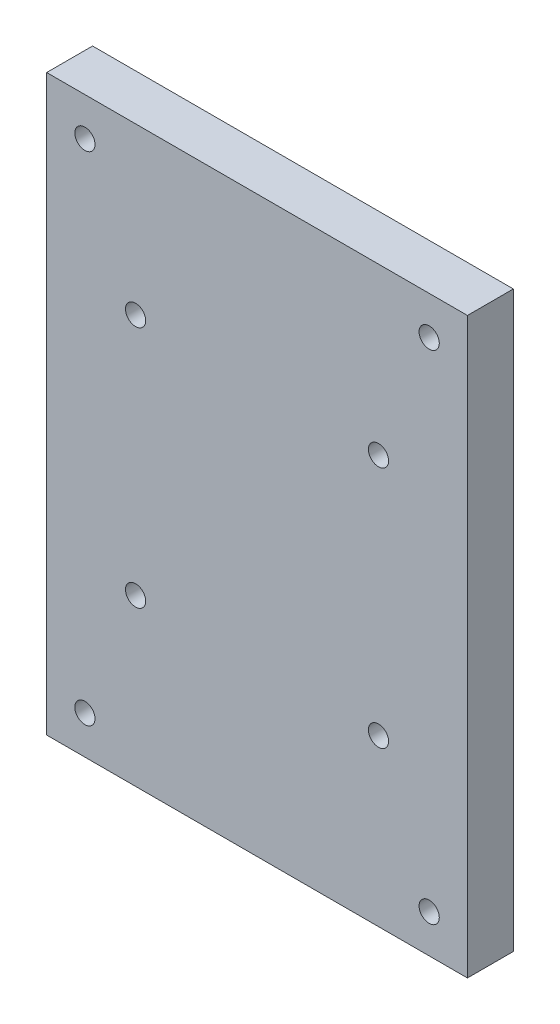
SolidWorks part; units mm, degrees
ref_plane "Front Plane" through (0, 0, 0) normal (0, 0, 1) x (1, 0, 0)
ref_plane "Top Plane" through (0, 0, 0) normal (0, 1, 0) x (1, 0, 0)
ref_plane "Right Plane" through (0, 0, 0) normal (1, 0, 0) x (0, 0, -1)
sketch "Sketch1" plane through (0, 0, 0) normal (0, 0, 1) x (1, 0, 0)
  line L0 (-55, 0) -> (0, -75) construction
  line L1 (0, 0) -> (-55, 0)
  line L2 (0, 0) -> (0, -75)
  line L3 (0, -75) -> (-55, -75)
  line L4 (-55, 0) -> (-55, -75)
  line L5 (0, 0) -> (-55, -75) construction
  line L6 (-27.5, -37.5) -> (-27.5, -26.0057) construction
  line L7 (-43.375, -21.625) -> (-11.625, -21.625) construction
  line L8 (-11.625, -21.625) -> (-11.625, -53.375) construction
  line L9 (-11.625, -53.375) -> (-43.375, -53.375) construction
  line L10 (-43.375, -53.375) -> (-43.375, -21.625) construction
  line L11 (-43.375, -21.625) -> (-11.625, -53.375) construction
  line L12 (-11.625, -53.375) -> (-27.5, -37.5) construction
  line L13 (-50, -70) -> (-5, -70) construction
  line L14 (-5, -70) -> (-5, -5) construction
  line L15 (-5, -5) -> (-50, -5) construction
  line L16 (-50, -5) -> (-50, -70) construction
  circle A0 centre (-43.375, -21.625) radius 1.32
  circle A1 centre (-11.625, -21.625) radius 1.32
  circle A2 centre (-11.625, -53.375) radius 1.32
  circle A3 centre (-43.375, -53.375) radius 1.32
  circle A4 centre (-50, -5) radius 1.32
  circle A5 centre (-5, -5) radius 1.32
  circle A6 centre (-5, -70) radius 1.32
  circle A7 centre (-50, -70) radius 1.32
  dimension "D3" = 2.64
  dimension "D8" = 5
  dimension "D9" = 5
  dimension "D10" = 2.64
  dimension "D13" = 45
  dimension "D14" = 65
  dimension "D1" = 55
  dimension "D2" = 75
  dimension "D6" = 31.75
  dimension "D7" = 31.75
  dimension "D4" = 2
  dimension "D5" = 2
  dimension "D11" = 2
  dimension "D12" = 2
extrude "Boss-Extrude1" add sketch "Sketch1" along normal blind 6
sketch "Sketch2" plane through (0, 0, 0) normal (0, 0, -1) x (-1, 0, 0)
  circle A0 centre (11.625, -21.625) radius 3.25
  circle A1 centre (43.375, -21.625) radius 3.25
  circle A2 centre (43.375, -53.375) radius 3.25
  circle A3 centre (11.625, -53.375) radius 3.25
  dimension "D1" = 6.5
  dimension "D2" = 2
  dimension "D3" = 2
extrude "Cut-Extrude1" cut sketch "Sketch2" against normal blind 4
